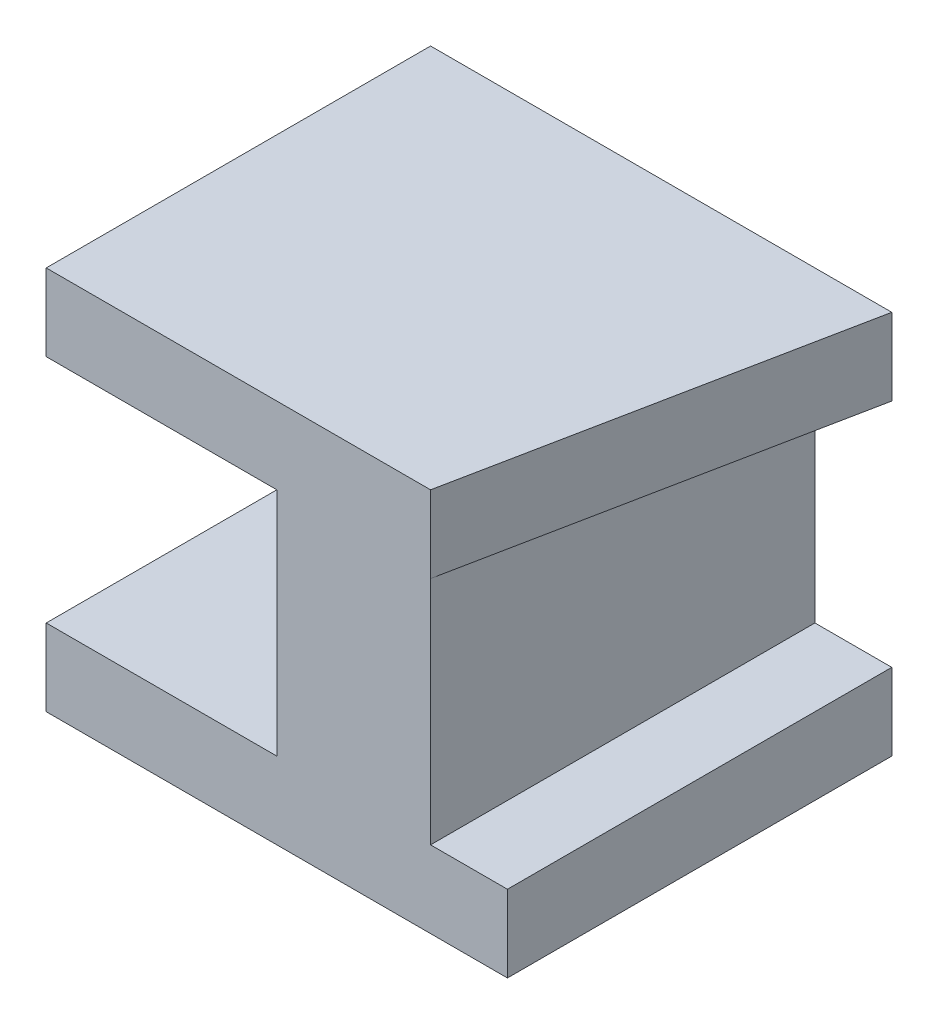
SolidWorks part; units mm, degrees
ref_plane "Front Plane" through (0, 0, 0) normal (0, 0, 1) x (1, 0, 0)
ref_plane "Top Plane" through (0, 0, 0) normal (0, 1, 0) x (1, 0, 0)
ref_plane "Right Plane" through (0, 0, 0) normal (1, 0, 0) x (0, 0, -1)
sketch "Sketch1" plane through (0, 0, 0) normal (0, 0, 1) x (1, 0, 0)
  line L0 (0, 0) -> (25, 0)
  line L1 (25, 0) -> (25, 25)
  line L2 (25, 25) -> (0, 25)
  line L3 (0, 25) -> (0, 20)
  line L4 (0, 20) -> (15, 20)
  line L5 (15, 20) -> (15, 5)
  line L6 (15, 5) -> (0, 5)
  line L7 (0, 5) -> (0, 0)
  dimension "D1" = 25
  dimension "D2" = 5
  dimension "D3" = 5
  dimension "D4" = 25
  dimension "D5" = 15
extrude "Boss-Extrude1" add sketch "Sketch1" along normal blind 25
sketch "Sketch2" plane through (15, 0, 0) normal (-1, 0, 0) x (0, 0, 1)
  line L0 (25, 20) -> (0, 20) construction
  line L1 (0, 5) -> (10, 5)
  line L2 (0, 5) -> (0, 20)
  line L3 (0, 20) -> (10, 20)
  line L4 (10, 5) -> (10, 20)
  dimension "D1" = 10
extrude "Boss-Extrude2" add sketch "Sketch2" along normal blind 10
sketch "Sketch3" plane through (25, 0, 0) normal (1, 0, 0) x (0, 0, -1)
  line L0 (0, 0) -> (0, 25) construction
  line L1 (-25, 25) -> (0, 25)
  line L2 (-25, 25) -> (-25, 20)
  line L3 (-25, 20) -> (0, 20)
  line L4 (0, 25) -> (0, 20)
  line L6 (-25, 0) -> (0, 0)
  line L7 (-25, 0) -> (-25, 5)
  line L8 (-25, 5) -> (0, 5)
  line L9 (0, 0) -> (0, 5)
  dimension "D1" = 5
  dimension "D2" = 5
extrude "Boss-Extrude3" add sketch "Sketch3" along normal blind 5
sketch "Sketch4" plane through (0, 25, 0) normal (0, 1, 0) x (1, 0, 0)
  line L0 (25, -25) -> (30, 0)
  line L1 (30, -25) -> (0, -25) construction
  line L2 (30, 0) -> (30, -25)
  line L3 (30, -25) -> (25, -25)
  dimension "D1" = 5
extrude "Cut-Extrude1" cut sketch "Sketch4" against normal blind 5
